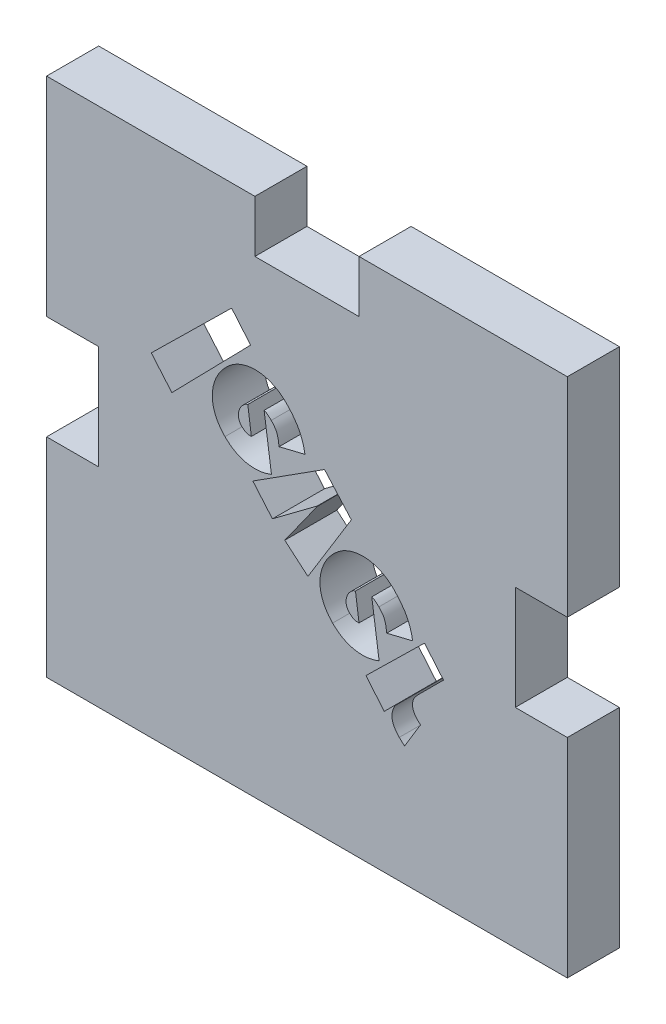
SolidWorks part; units mm, degrees
ref_plane "Front Plane" through (0, 0, 0) normal (0, 0, 1) x (1, 0, 0)
ref_plane "Top Plane" through (0, 0, 0) normal (0, 1, 0) x (1, 0, 0)
ref_plane "Right Plane" through (0, 0, 0) normal (1, 0, 0) x (0, 0, -1)
sketch "Sketch1" plane through (0, 0, 0) normal (0, 0, 1) x (1, 0, 0)
  line L0 (0, -31.75) -> (0, 31.75) construction
  line L1 (-15.875, 15.875) -> (-3.175, 15.875)
  line L2 (-15.875, 15.875) -> (-15.875, 3.175)
  line L3 (0, 0) -> (35.3222, 0) construction
  line L4 (-3.175, -15.875) -> (3.175, -15.875)
  line L6 (-15.875, 3.175) -> (-12.7, 3.175)
  line L7 (-12.7, 3.175) -> (-12.7, -3.175)
  line L8 (-12.7, -3.175) -> (-15.875, -3.175)
  line L9 (15.875, 15.875) -> (15.875, 3.175)
  line L10 (15.875, 15.875) -> (3.175, 15.875)
  line L11 (15.875, 3.175) -> (12.7, 3.175)
  line L13 (15.875, -15.875) -> (3.175, -15.875)
  line L15 (15.875, -15.875) -> (15.875, -3.175)
  line L16 (12.7, 3.175) -> (12.7, -3.175)
  line L17 (12.7, -3.175) -> (15.875, -3.175)
  line L20 (-15.875, -15.875) -> (-15.875, -3.175)
  line L21 (-15.875, -15.875) -> (-3.175, -15.875)
  line L22 (-3.175, 15.875) -> (-3.175, 12.7)
  line L23 (-3.175, 12.7) -> (3.175, 12.7)
  line L24 (3.175, 12.7) -> (3.175, 15.875)
  point P18 (-38.1, 0)
  point P26 (38.1, 0)
  dimension "D1" = 3.175
  dimension "D2" = 3.175
  dimension "D4" = 6.35
  dimension "D5" = 31.75
  dimension "D6" = 3.175
  dimension "D7" = 31.75
  dimension "D8" = 3.175
extrude "Extrude1" add sketch "Sketch1" along normal blind 3.175
sketch "Sketch2" plane through (0, 0, 3.175) normal (0, 0, 1) x (1, 0, 0)
  line L0 (-15.875, 15.875) -> (15.875, -15.875) construction
  line L1 (-15.875, -15.875) -> (15.875, -15.875) construction
  line L2 (15.875, -15.875) -> (15.875, -3.175) construction
  line L3 (-15.875, 11.3277) -> (11.3277, -15.875) construction
  line L4 (-15.875, 15.875) -> (-15.875, 3.175) construction
  line L5 (-11.3277, 15.875) -> (15.875, -11.3277) construction
  text T0 "lever" font "GROBOLD" height in points 28
extrude "Cut-Extrude1" cut sketch "Sketch2" against normal through all
